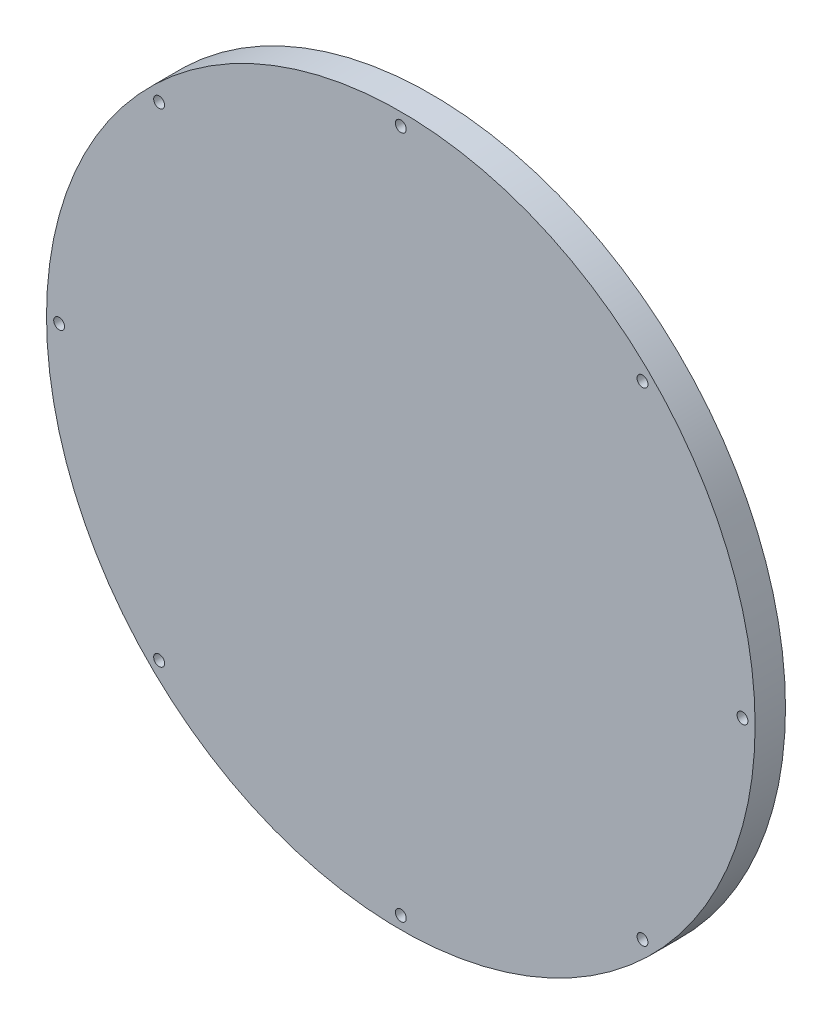
SolidWorks part; units mm, degrees
material "6061-T6 (SS)"
ref_plane "Front" through (0, 0, 0) normal (0, 0, 1) x (1, 0, 0)
ref_plane "Top" through (0, 0, 0) normal (0, 1, 0) x (1, 0, 0)
ref_plane "Right" through (0, 0, 0) normal (1, 0, 0) x (0, 0, -1)
sketch "Sketch1" plane through (0, 0, 0) normal (0, 0, 1) x (1, 0, 0)
  circle A0 centre (0, 0) radius 140
extrude "Boss-Extrude1" add sketch "Sketch1" along normal blind 12
hole_wizard "CSK for M4 Flat Head Machine Screw1" positions "Sketch2" profile "Sketch3" countersink size "M4" standard "ANSI Metric" end condition through all
sketch "Sketch2" plane through (0, 0, 0) normal (0, 0, -1) x (-1, 0, 0)
  point P0 (0, 135)
  point P2 (135, 0)
  point P4 (0, -135)
  point P6 (-135, 0)
  point P16 (-95.5, 95.5)
  point P18 (95.5, 95.5)
  point P20 (95.5, -95.5)
  point P22 (-95.5, -95.5)
sketch "Sketch3" plane through (0, 135, 0) normal (1, 0, 0) x (0, 1, 0)
  line L0 (0, 0) -> (0, 12)
  line L1 (0, 12) -> (2.15, 12)
  line L2 (2.15, 12) -> (2.15, 2.55)
  line L3 (2.15, 2.55) -> (4.7, 0)
  line L5 (4.7, 0) -> (0, 0)
  line L6 (-2.15, 2.55) -> (-4.7, 0) construction
  line L11 (0, -6.35) -> (0, 107.95) construction
  dimension "Thru Hole Dia." = 4.3
  dimension "Thru Hole Depth" = 12
  dimension "Near C'Sink Dia." = 9.4
  dimension "Near C'Sink Angle" = 90
